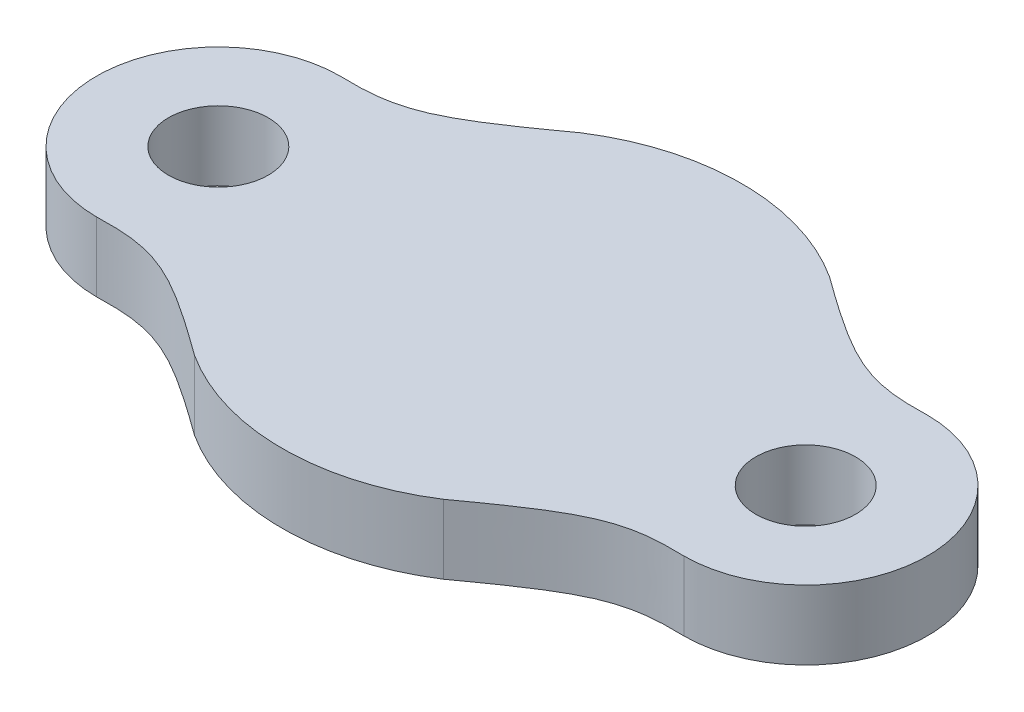
SolidWorks part; units mm, degrees
ref_plane "Alzado" through (0, 0, 0) normal (0, 0, 1) x (1, 0, 0)
ref_plane "Planta" through (0, 0, 0) normal (0, 1, 0) x (1, 0, 0)
ref_plane "Vista lateral" through (0, 0, 0) normal (1, 0, 0) x (0, 0, -1)
sketch "Croquis1" plane through (0, 0, 0) normal (0, 1, 0) x (1, 0, 0)
  line L0 (-7.0513, 8.8693) -> (-7.0513, -10.2233) construction
  line L1 (-18.4349, 0) -> (5.0713, 0) construction
  circle A0 centre (-13.7823, 0) radius 2.794
  circle A2 centre (-13.7823, 0) radius 1.143
  circle A4 centre (-7.0513, 0) radius 5.2625
  circle A5 centre (-0.3203, 0) radius 1.143
  circle A6 centre (-0.3203, 0) radius 2.794
  spline S0 degree 3 poles (-13.7823, 2.794) (-12.382, 2.7452) (-11.8084, 3.0432) (-9.9062, 4.4208) knots 0 0 0 0 1 1 1 1
  spline S1 degree 3 poles (-13.7823, -2.794) (-12.382, -2.7452) (-11.8084, -3.0432) (-9.9062, -4.4208) knots 0 0 0 0 1 1 1 1
  spline S2 degree 3 poles (-0.3203, -2.794) (-1.7207, -2.7452) (-2.2942, -3.0432) (-4.1964, -4.4208) knots 0 0 0 0 1 1 1 1
  spline S3 degree 3 poles (-0.3203, 2.794) (-1.7207, 2.7452) (-2.2942, 3.0432) (-4.1964, 4.4208) knots 0 0 0 0 1 1 1 1
  dimension "D6" = 0
  dimension "D1" = 10.525
extrude "Saliente-Extruir6" add sketch "Croquis1" along normal blind 1.5875 contours A6 S3 A4 S2 A5 | A6 A4 | A6 S3 A4 | S2 A6 A4 | A4 S3 S0 A0 S1 S2 A6 | A0 S1 A4 | A0 A4 | A0 S1 A4 S0 A2 | S0 A0 A4
